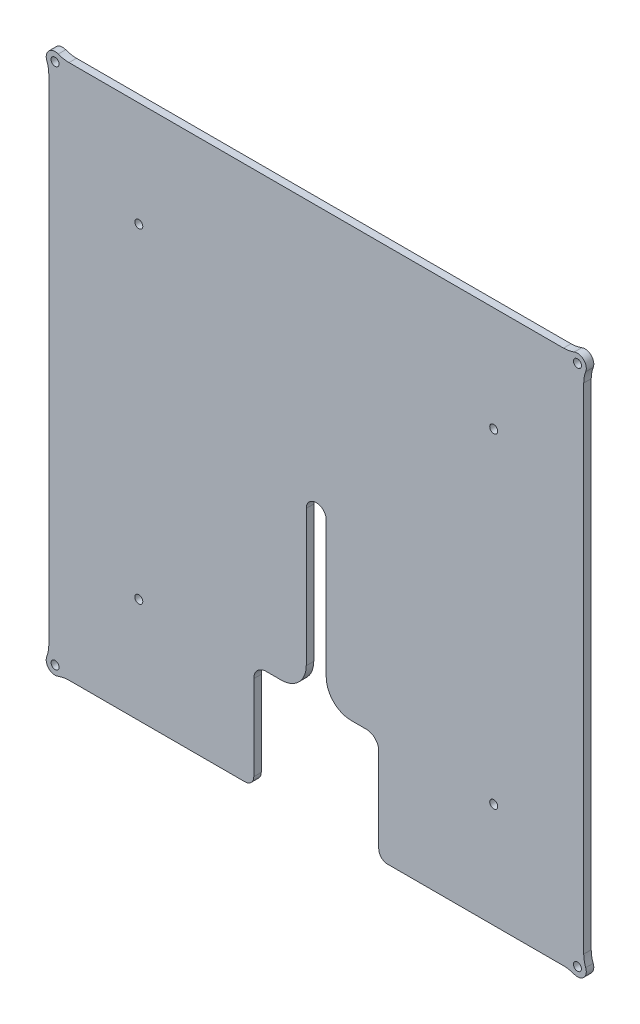
SolidWorks part; units mm, degrees
material "Balsa"
ref_plane "Front Plane" through (0, 0, 0) normal (0, 0, 1) x (1, 0, 0)
ref_plane "Top Plane" through (0, 0, 0) normal (0, 1, 0) x (1, 0, 0)
ref_plane "Right Plane" through (0, 0, 0) normal (1, 0, 0) x (0, 0, -1)
sketch "Sketch1" plane through (0, 0, 0) normal (0, 0, 1) x (1, 0, 0)
  line L0 (-107, 98.923) -> (-107, -98.923)
  line L1 (98.923, 107) -> (-98.923, 107)
  line L2 (107, -98.923) -> (107, 98.923)
  line L3 (43, -107) -> (98.923, -107)
  line L4 (43, -107) -> (43, -101) construction
  line L5 (39, -97) -> (-39, -97) construction
  line L6 (-43, -101) -> (-43, -107) construction
  line L7 (-98.923, -107) -> (-43, -107)
  line L8 (-43, -107) -> (43, -107)
  line L9 (104.5, -104.5) -> (-104.5, -104.5) construction
  line L10 (104.5, -104.5) -> (104.5, 104.5) construction
  line L11 (104.5, 104.5) -> (-104.5, 104.5) construction
  line L12 (-104.5, -104.5) -> (-104.5, 104.5) construction
  line L13 (104.5, -104.5) -> (-104.5, 104.5) construction
  line L14 (104.5, 104.5) -> (-104.5, -104.5) construction
  circle A0 centre (-104.5, -104.5) radius 1.6
  circle A1 centre (-104.5, 104.5) radius 1.6
  circle A2 centre (104.5, 104.5) radius 1.6
  circle A3 centre (104.5, -104.5) radius 1.6
  arc A4 (43, -101) -> (39, -97) centre (39, -101) ccw construction
  arc A5 (-39, -97) -> (-43, -101) centre (-39, -101) ccw construction
  arc A6 (-103.2308, 107.7999) -> (-107.7999, 103.2308) centre (-104.5, 104.5) ccw
  arc A8 (-107.7999, -103.2308) -> (-103.2308, -107.7999) centre (-104.5, -104.5) ccw
  arc A9 (98.923, -107) -> (103.2308, -107.7999) centre (98.923, -119) cw
  arc A10 (103.2308, -107.7999) -> (107.7999, -103.2308) centre (104.5, -104.5) ccw
  arc A13 (107.7999, 103.2308) -> (103.2308, 107.7999) centre (104.5, 104.5) ccw
  arc A14 (107, -98.923) -> (107.7999, -103.2308) centre (119, -98.923) ccw
  arc A15 (-103.2308, -107.7999) -> (-98.923, -107) centre (-98.923, -119) cw
  arc A16 (-107, -98.923) -> (-107.7999, -103.2308) centre (-119, -98.923) cw
  arc A17 (-107.7999, 103.2308) -> (-107, 98.923) centre (-119, 98.923) cw
  arc A18 (-103.2308, 107.7999) -> (-98.923, 107) centre (-98.923, 119) ccw
  arc A19 (107, 98.923) -> (107.7999, 103.2308) centre (119, 98.923) cw
  arc A20 (103.2308, 107.7999) -> (98.923, 107) centre (98.923, 119) cw
  point P0 (0, 0)
  dimension "D1" = 12
  dimension "D3" = 12
  dimension "D4" = 12
  dimension "D5" = 12
  dimension "D6" = 12
  dimension "D7" = 12
  dimension "D2" = 209
  dimension "D8" = 214
  dimension "D9" = 10
extrude "Boss-Extrude1" add sketch "Sketch1" along normal blind 3
sketch "Sketch3" plane through (0, 0, 3) normal (0, 0, 1) x (1, 0, 0)
  line L0 (-107, 98.923) -> (-107, -98.923) construction
  line L1 (71, -65) -> (-71, -65) construction
  line L2 (71, -65) -> (71, 65) construction
  line L3 (71, 65) -> (-71, 65) construction
  line L4 (-71, -65) -> (-71, 65) construction
  line L5 (71, -65) -> (-71, 65) construction
  line L6 (71, 65) -> (-71, -65) construction
  line L8 (98.923, 107) -> (-98.923, 107) construction
  circle A0 centre (-71, 65) radius 1.6
  circle A1 centre (71, 65) radius 1.6
  circle A2 centre (71, -65) radius 1.6
  circle A3 centre (-71, -65) radius 1.6
  point P0 (0, 0)
  dimension "D3" = 3.2
  dimension "D1" = 36
  dimension "D2" = 130
extrude "Cut-Extrude2" cut sketch "Sketch3" against normal through all
sketch "Sketch5" plane through (0, 0, 0) normal (0, 0, 1) x (1, 0, 0)
  line L0 (-107, 98.923) -> (-107, -98.923) construction
  line L3 (-98.923, -107) -> (98.923, -107) construction
  line L4 (-25, -107) -> (25, -107)
  line L5 (107, -98.923) -> (107, 98.923) construction
  line L6 (-107, 98.923) -> (-107, -98.923) construction
  line L7 (107, -98.923) -> (107, 98.923) construction
  line L12 (4, 0) -> (4, -54.5)
  line L13 (-4, 0) -> (-4, -54.5)
  line L14 (-14, -64.5) -> (-20, -64.5)
  line L15 (-25, -69.5) -> (-25, -107)
  line L16 (20, -112) -> (-20, -112) construction
  line L17 (25, -69.5) -> (25, -107)
  line L18 (20, -64.5) -> (14, -64.5)
  line L19 (0, 0) -> (0, -112) construction
  arc A15 (4, -54.5) -> (14, -64.5) centre (14, -54.5) ccw
  arc A16 (4, 0) -> (-4, 0) centre (0, 0) ccw
  arc A17 (-14, -64.5) -> (-4, -54.5) centre (-14, -54.5) ccw
  arc A18 (-20, -64.5) -> (-25, -69.5) centre (-20, -69.5) ccw
  arc A19 (-25, -107) -> (-20, -112) centre (-20, -107) ccw construction
  arc A20 (20, -112) -> (25, -107) centre (20, -107) ccw construction
  arc A21 (25, -69.5) -> (20, -64.5) centre (20, -69.5) ccw
  dimension "D4" = 8
  dimension "D5" = 10
  dimension "D6" = 5
  dimension "D1" = 50
  dimension "D2" = 64.5
  dimension "D3" = 107
extrude "Cut-Extrude5" cut sketch "Sketch5" along normal through all
fillet "Fillet1" radius 3.54 2 edges at (-25, -107, 1.5) (25, -107, 1.5)
